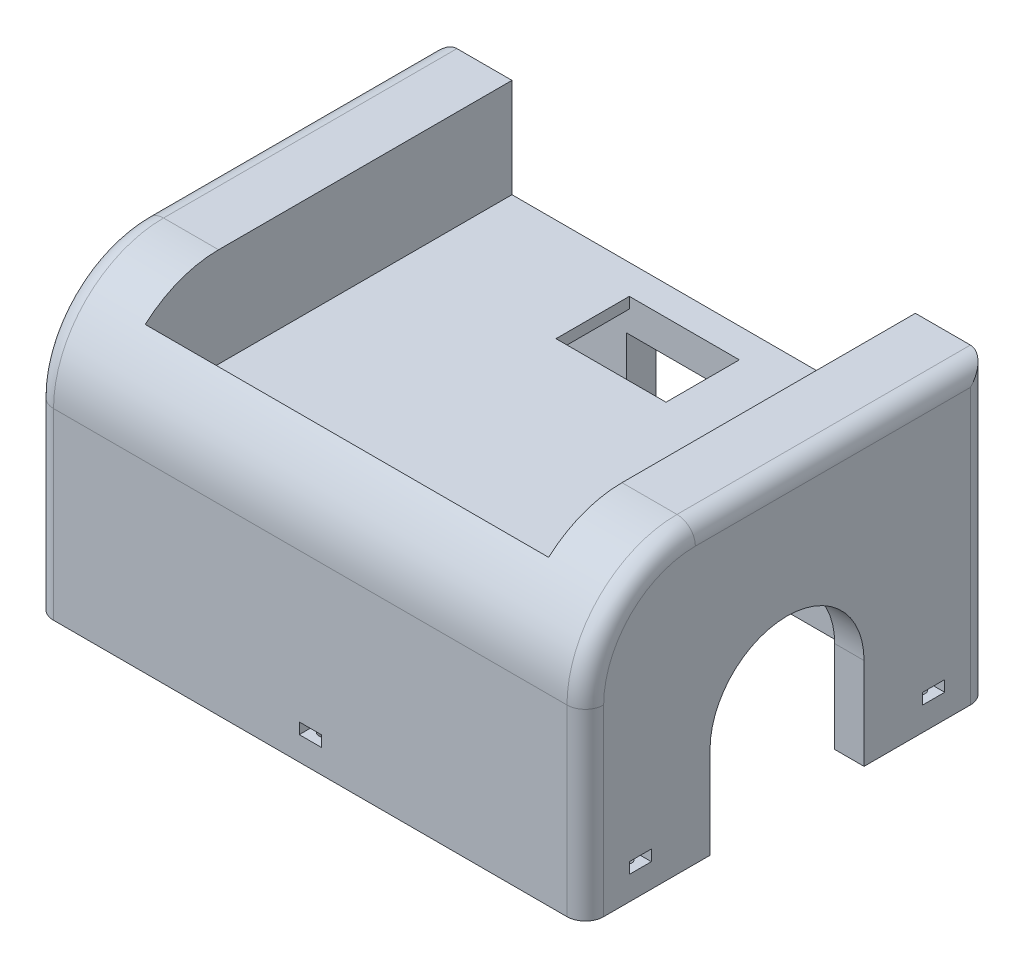
SolidWorks part; units mm, degrees
ref_plane "前视基准面" through (0, 0, 0) normal (0, 0, 1) x (1, 0, 0)
ref_plane "上视基准面" through (0, 0, 0) normal (0, 1, 0) x (1, 0, 0)
ref_plane "右视基准面" through (0, 0, 0) normal (1, 0, 0) x (0, 0, -1)
sketch "草图1" plane through (0, 0, 0) normal (0, 1, 0) x (1, 0, 0)
  line L1 (-75, 55) -> (75, 55)
  line L2 (-75, 55) -> (-75, -55)
  line L3 (-75, -55) -> (75, -55)
  line L4 (75, 55) -> (75, -55)
  line L5 (-75, 55) -> (75, -55) construction
  line L6 (-75, -55) -> (75, 55) construction
  point P0 (0, 0)
  dimension "D1" = 150
  dimension "D2" = 110
extrude "凸台-拉伸1" add sketch "草图1" along normal blind 80
fillet "圆角3" radius 30 1 edges at (0, 80, 55)
fillet "圆角1" radius 5 8 edges at (-75, 40, -55) (75, 40, -55) (75, 25, 55) (-75, 25, 55) (75, 80, -15) (75, 71.2132, 46.2132) (-75, 80, -15) (-75, 71.2132, 46.2132)
sketch "草图2" plane through (75, 0, 0) normal (1, 0, 0) x (0, 0, -1)
  line L0 (-21, 25) -> (-21, 0)
  line L1 (-50, 0) -> (50, 0) construction
  line L2 (-21, 0) -> (21, 0)
  line L3 (21, 0) -> (21, 25)
  arc A0 (21, 25) -> (-21, 25) centre (0, 25) ccw
  dimension "D1" = 42
  dimension "D2" = 25
extrude "切除-拉伸1" cut sketch "草图2" against normal through all
sketch "草图3" plane through (0, 0, -55) normal (0, 0, -1) x (-1, 0, 0)
  line L0 (-25, 0) -> (25, 0)
  line L1 (-25, 18) -> (25, 18)
  line L2 (-25, 18) -> (-25, 0)
  line L4 (25, 18) -> (25, 0)
  line L5 (-25, 18) -> (25, -18) construction
  line L6 (-25, -18) -> (25, 18) construction
  point P0 (0, 0)
  dimension "D1" = 50
  dimension "D2" = 36
extrude "切除-拉伸2" cut sketch "草图3" against normal blind 50
sketch "草图4" plane through (0, 0, 0) normal (0, -1, 0) x (1, 0, 0)
  line L0 (75, -21) -> (75, -50) construction
  line L1 (67, -47) -> (-67, -47)
  line L2 (67, -47) -> (67, 47)
  line L3 (67, 47) -> (-67, 47)
  line L4 (-67, -47) -> (-67, 47)
  line L5 (67, -47) -> (-67, 47) construction
  line L6 (67, 47) -> (-67, -47) construction
  line L7 (70, -55) -> (25, -55) construction
  point P0 (0, 0)
  dimension "D1" = 8
  dimension "D2" = 8
extrude "切除-拉伸3" cut sketch "草图4" against normal blind 50
sketch "草图5" plane through (0, 80, 0) normal (0, 1, 0) x (1, 0, 0)
  line L0 (70, 55) -> (-70, 55) construction
  line L5 (55, -45) -> (-55, -45)
  line L6 (55, -45) -> (55, 55)
  line L7 (55, 55) -> (-55, 55)
  line L8 (-55, -45) -> (-55, 55)
  line L9 (55, -45) -> (-55, 55) construction
  line L10 (55, 55) -> (-55, -45) construction
  point P0 (0, 5)
  dimension "D1" = 100
  dimension "D2" = 110
extrude "切除-拉伸4" cut sketch "草图5" against normal blind 27
sketch "草图6" plane through (0, 0, -55) normal (0, 0, -1) x (-1, 0, 0)
  line L0 (25, 18) -> (-25, 18) construction
  line L1 (-14.2589, 44) -> (15.7411, 44)
  line L2 (-14.2589, 44) -> (-14.2589, 24)
  line L3 (-14.2589, 24) -> (15.7411, 24)
  line L4 (15.7411, 44) -> (15.7411, 24)
  line L5 (-14.2589, 44) -> (15.7411, 24) construction
  line L6 (-14.2589, 24) -> (15.7411, 44) construction
  point P0 (0.7411, 34)
  dimension "D1" = 20
  dimension "D2" = 30
  dimension "D3" = 16
extrude "切除-拉伸5" cut sketch "草图6" against normal blind 23.3
sketch "草图7" plane through (0, 53, 0) normal (0, 1, 0) x (1, 0, 0)
  line L0 (55, 55) -> (-55, 55) construction
  line L1 (15, 27) -> (-15, 27)
  line L2 (15, 27) -> (15, 47)
  line L3 (15, 47) -> (-15, 47)
  line L4 (-15, 27) -> (-15, 47)
  line L5 (15, 27) -> (-15, 47) construction
  line L6 (15, 47) -> (-15, 27) construction
  point P0 (0, 37)
  dimension "D1" = 30
  dimension "D2" = 20
  dimension "D3" = 8
extrude "切除-拉伸6" cut sketch "草图7" against normal blind 23.3 contours L2 L3 L4 L1
sketch "草图8" plane through (0, 0, 0) normal (0, -1, 0) x (1, 0, 0)
  line L0 (148.3812, 0) -> (0, 0) construction
  line L1 (0, 0) -> (-155.7322, 0) construction
  line L2 (0, -100.872) -> (0, 0) construction
  line L3 (75, 50) -> (75, 21) construction
  line L4 (-70, 55) -> (70, 55) construction
  line L5 (0, 51) -> (0, 0) construction
  circle A0 centre (71, 40) radius 1.65
  circle A1 centre (71, -40) radius 1.65
  circle A2 centre (-71, -40) radius 1.65
  circle A3 centre (-71, 40) radius 1.65
  circle A4 centre (0, 51) radius 1.65
  dimension "D1" = 3.3
  dimension "D2" = 4
  dimension "D3" = 40
  dimension "D4" = 3.3
  dimension "D5" = 4
extrude "切除-拉伸7" cut sketch "草图8" against normal blind 10
sketch "草图11" plane through (-75, 0, 0) normal (-1, 0, 0) x (0, 0, 1)
  line L0 (0, 0) -> (0, 120.5929) construction
  line L1 (-40, 10) -> (-40, 0) construction
  line L2 (-41.65, 10) -> (-38.35, 10) construction
  line L3 (-50, 0) -> (-21, 0) construction
  line L4 (43, 6.5) -> (37, 9.5) construction
  line L5 (-43, 9.5) -> (-37, 9.5)
  line L6 (-43, 9.5) -> (-43, 6.5)
  line L7 (-43, 6.5) -> (-37, 6.5)
  line L8 (-37, 9.5) -> (-37, 6.5)
  line L9 (-43, 9.5) -> (-37, 6.5) construction
  line L10 (-43, 6.5) -> (-37, 9.5) construction
  line L11 (43, 9.5) -> (37, 6.5) construction
  line L12 (40, 10) -> (40, 0) construction
  line L13 (37, 9.5) -> (37, 6.5)
  line L14 (43, 6.5) -> (37, 6.5)
  line L15 (43, 9.5) -> (43, 6.5)
  line L16 (43, 9.5) -> (37, 9.5)
  point P9 (-40, 8)
  point P20 (40, 8)
  dimension "D1" = 6
  dimension "D2" = 3
  dimension "D3" = 8
extrude "切除-拉伸8" cut sketch "草图11" against normal blind 161
sketch "草图12" plane through (0, 0, 55) normal (0, 0, 1) x (1, 0, 0)
  line L0 (0, 0) -> (0, 10) construction
  line L1 (-1.65, 10) -> (1.65, 10) construction
  line L2 (-70, 0) -> (70, 0) construction
  line L3 (-3, 9.5) -> (3, 9.5)
  line L4 (-3, 9.5) -> (-3, 6.5)
  line L5 (-3, 6.5) -> (3, 6.5)
  line L6 (3, 9.5) -> (3, 6.5)
  line L7 (-3, 9.5) -> (3, 6.5) construction
  line L8 (-3, 6.5) -> (3, 9.5) construction
  point P5 (0, 8)
  dimension "D1" = 6
  dimension "D2" = 3
  dimension "D3" = 8
extrude "切除-拉伸9" cut sketch "草图12" against normal blind 161
